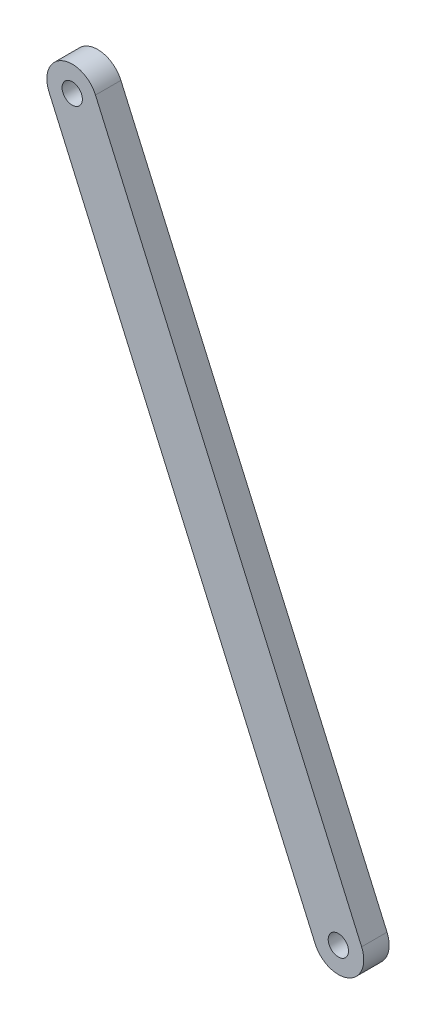
SolidWorks part; units mm, degrees
ref_plane "Front Plane" through (0, 0, 0) normal (0, 0, 1) x (1, 0, 0)
ref_plane "Top Plane" through (0, 0, 0) normal (0, 1, 0) x (1, 0, 0)
ref_plane "Right Plane" through (0, 0, 0) normal (1, 0, 0) x (0, 0, -1)
sketch "Sketch1" plane through (0, 0, 0) normal (0, 0, 1) x (1, 0, 0)
  line L2 (-65.6441, 162.8002) -> (-13.2752, 43.815) construction
  line L3 (-22.4279, 39.7866) -> (-74.7968, 158.7719) construction
  line L4 (-65.6441, 162.8002) -> (-13.2752, 43.815)
  line L5 (-22.4279, 39.7866) -> (-74.7968, 158.7719)
  circle A6 centre (-70.2204, 160.7861) radius 2 construction
  circle A7 centre (-17.8515, 41.8008) radius 2 construction
  arc A8 (-22.4279, 39.7866) -> (-13.2752, 43.815) centre (-17.8515, 41.8008) ccw construction
  arc A9 (-65.6441, 162.8002) -> (-74.7968, 158.7719) centre (-70.2204, 160.7861) ccw construction
  circle A10 centre (-70.2204, 160.7861) radius 2
  circle A11 centre (-17.8515, 41.8008) radius 2
  arc A12 (-22.4279, 39.7866) -> (-13.2752, 43.815) centre (-17.8515, 41.8008) ccw
  arc A13 (-65.6441, 162.8002) -> (-74.7968, 158.7719) centre (-70.2204, 160.7861) ccw
extrude "Boss-Extrude1" add sketch "Sketch1" along normal blind 5 from offset 5
